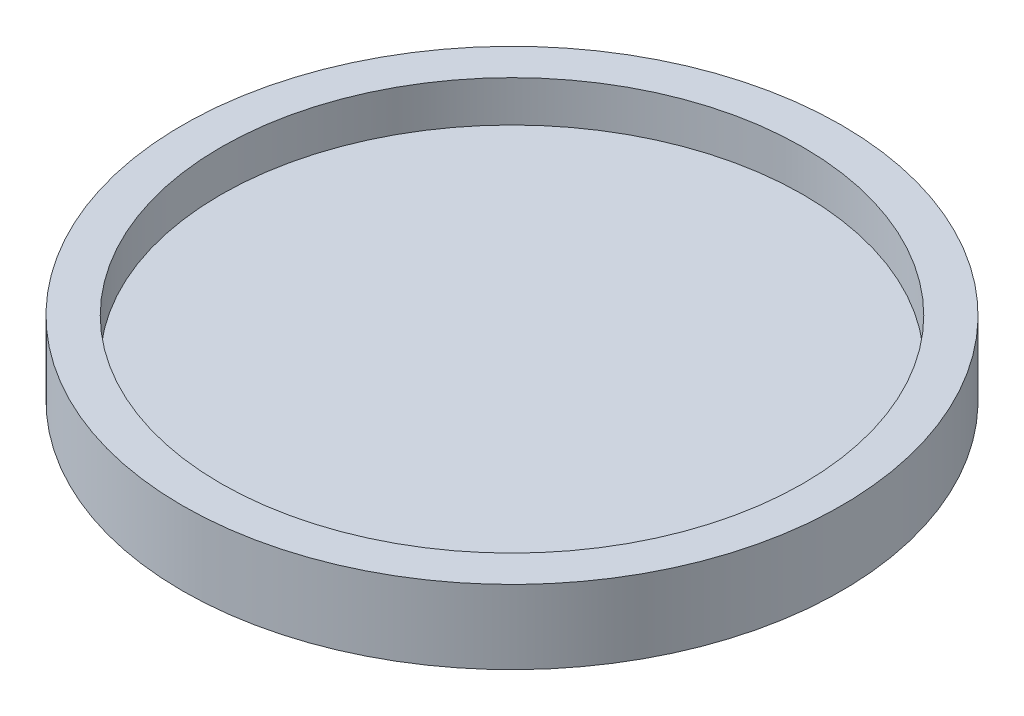
SolidWorks part; units mm, degrees
ref_plane "Front Plane" through (0, 0, 0) normal (0, 0, 1) x (1, 0, 0)
ref_plane "Top Plane" through (0, 0, 0) normal (0, 1, 0) x (1, 0, 0)
ref_plane "Right Plane" through (0, 0, 0) normal (1, 0, 0) x (0, 0, -1)
sketch "Sketch1" plane through (0, 0, 0) normal (0, 1, 0) x (1, 0, 0)
  circle A0 centre (0, 0) radius 51.0286
  circle A1 centre (0, 0) radius 45.085
  dimension "D1" = 90.17
  dimension "D2" = 5.9436
extrude "Boss-Extrude1" add sketch "Sketch1" along normal blind 6.35
sketch "Sketch2" plane through (0, 0, 0) normal (0, -1, 0) x (1, 0, 0)
  circle A0 centre (0, 0) radius 51.0286
  circle A4 centre (0, 0) radius 51.0286 construction
extrude "Boss-Extrude2" add sketch "Sketch2" along normal blind 5.08
